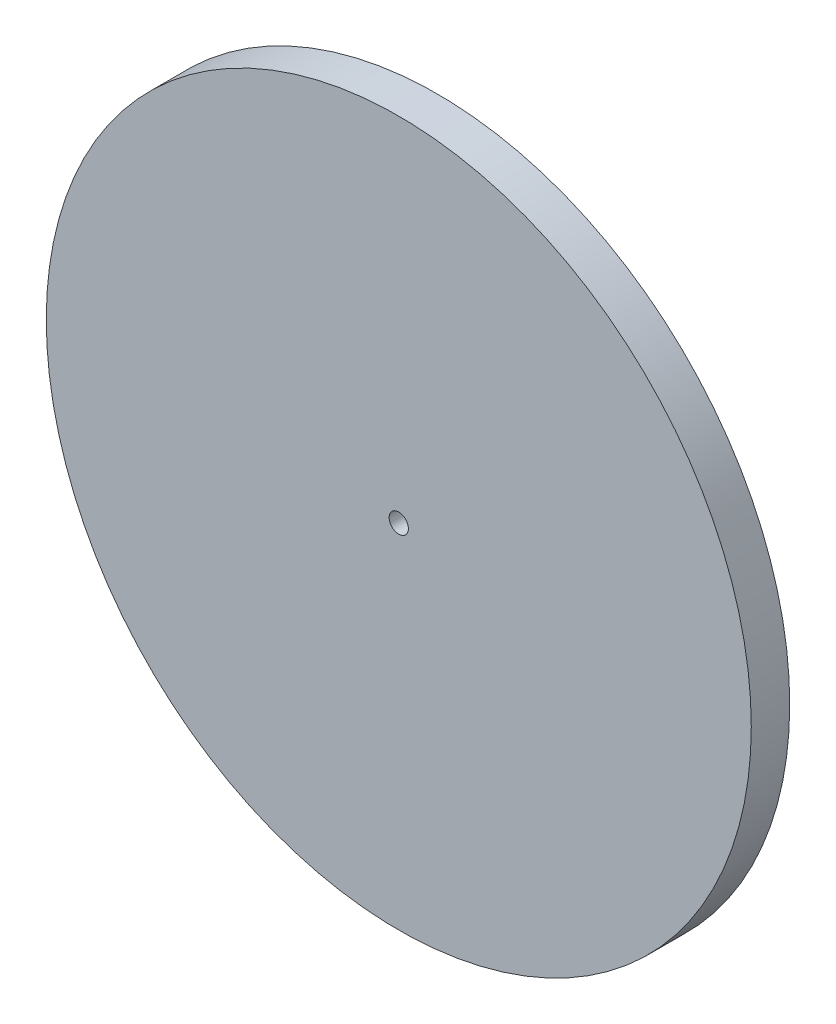
SolidWorks part; units mm, degrees
material "Free-Cutting Brass, UNS C36000"
ref_plane "Front Plane" through (0, 0, 0) normal (0, 0, 1) x (1, 0, 0)
ref_plane "Top Plane" through (0, 0, 0) normal (0, 1, 0) x (1, 0, 0)
ref_plane "Right Plane" through (0, 0, 0) normal (1, 0, 0) x (0, 0, -1)
sketch "Sketch1" plane through (0, 0, 0) normal (0, 0, 1) x (1, 0, 0)
  circle A0 centre (0, 0) radius 27.5
  circle A1 centre (0, 0) radius 0.75
  dimension "D1" = 55
  dimension "D2" = 1.5
extrude "Boss-Extrude1" add sketch "Sketch1" along normal blind 3
